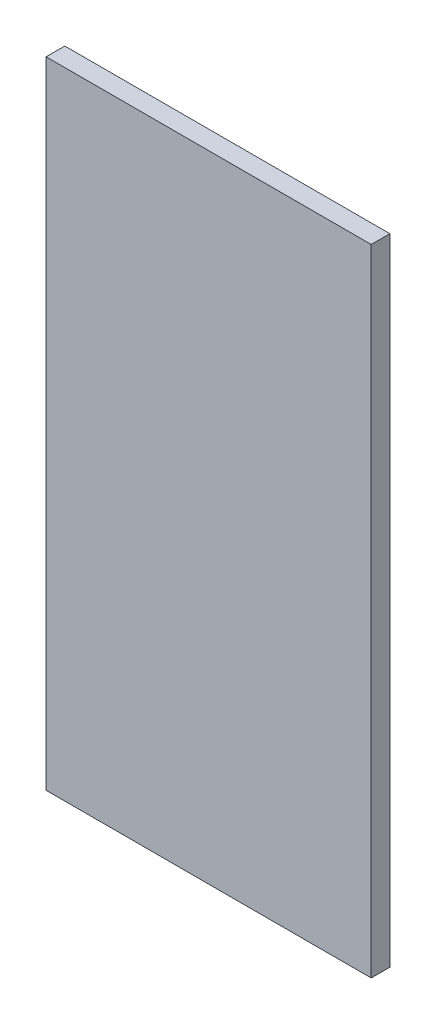
SolidWorks part; units mm, degrees
ref_plane "Front Plane" through (0, 0, 0) normal (0, 0, 1) x (1, 0, 0)
ref_plane "Top Plane" through (0, 0, 0) normal (0, 1, 0) x (1, 0, 0)
ref_plane "Right Plane" through (0, 0, 0) normal (1, 0, 0) x (0, 0, -1)
sketch "Sketch1" plane through (0, 0, 0) normal (0, 0, 1) x (1, 0, 0)
  line L0 (0, 0) -> (0, 170)
  line L1 (0, 170) -> (87, 170)
  line L2 (87, 170) -> (87, 0)
  line L3 (87, 0) -> (0, 0)
  dimension "D1" = 170
  dimension "D2" = 87
extrude "Boss-Extrude2" add sketch "Sketch1" along normal blind 5
